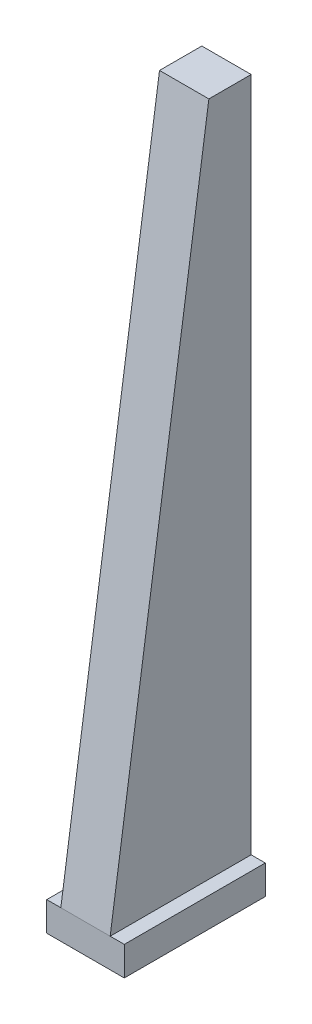
SolidWorks part; units mm, degrees
ref_plane "Front Plane" through (0, 0, 0) normal (0, 0, 1) x (1, 0, 0)
ref_plane "Top Plane" through (0, 0, 0) normal (0, 1, 0) x (1, 0, 0)
ref_plane "Right Plane" through (0, 0, 0) normal (1, 0, 0) x (0, 0, -1)
sketch "Sketch1" plane through (0, 0, 0) normal (0, 0, 1) x (1, 0, 0)
  line L0 (0, 0) -> (0, 2540) construction
  line L1 (88.9, 2540) -> (-88.9, 2540)
  line L2 (-88.9, 2540) -> (-88.9, 104.9604)
  line L3 (-88.9, 104.9604) -> (-139.7, 104.9604)
  line L4 (-139.7, 104.9604) -> (-139.7, 0)
  line L5 (-139.7, 0) -> (139.7, 0)
  line L6 (139.7, 104.9604) -> (139.7, 0)
  line L7 (88.9, 104.9604) -> (139.7, 104.9604)
  line L8 (88.9, 2540) -> (88.9, 104.9604)
  point P3 (-66.3539, 153.0394)
  dimension "D1" = 2540
  dimension "D2" = 139.7
  dimension "D3" = 104.9604
  dimension "D4" = 50.8
extrude "Boss-Extrude1" add sketch "Sketch1" along normal mid plane 508
sketch "Sketch2" plane through (0, 0, 0) normal (1, 0, 0) x (0, 0, -1)
  line L0 (101.6, 2540) -> (-254, 104.9604)
  line L1 (-254, 2540) -> (254, 2540) construction
  line L2 (-254, 2540) -> (-254, 104.9604) construction
  line L3 (-254, 2540) -> (-254, 104.9604)
  line L4 (-254, 2540) -> (254, 2540)
  point P2 (0, 0)
  dimension "D1" = 152.4
extrude "Cut-Extrude1" cut sketch "Sketch2" against normal through all both and the other way through all contours L4 L3 L0
